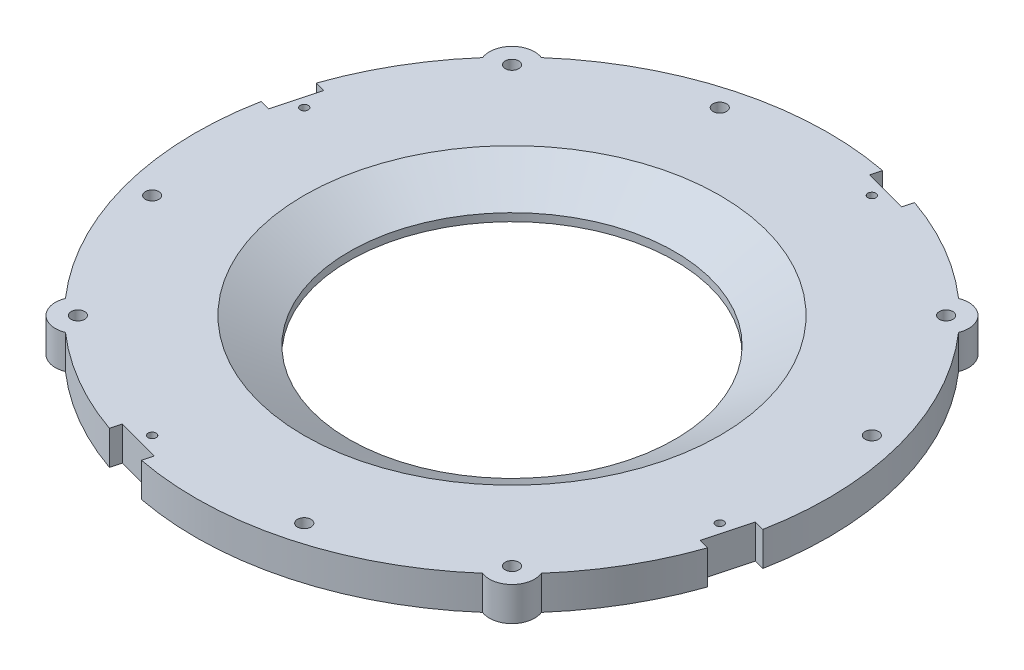
SolidWorks part; units mm, degrees
material "6061-T6 (SS)"
ref_plane "Front Plane" through (0, 0, 0) normal (0, 0, 1) x (1, 0, 0)
ref_plane "Top Plane" through (0, 0, 0) normal (0, 1, 0) x (1, 0, 0)
ref_plane "Right Plane" through (0, 0, 0) normal (1, 0, 0) x (0, 0, -1)
sketch "Sketch1" plane through (0, 0, 0) normal (0, 1, 0) x (1, 0, 0)
  line L0 (0, 88.9) -> (0, -88.9) construction
  line L1 (-88.9, 0) -> (88.9, 0) construction
  line L2 (-60.9759, -60.9759) -> (60.9759, 60.9759) construction
  line L3 (60.9759, -60.9759) -> (-60.9759, 60.9759) construction
  arc A0 (-66.8608, 58.5904) -> (-66.8608, -58.5904) centre (0, 0) ccw
  arc A1 (-58.5904, 66.8608) -> (-66.8608, 58.5904) centre (-60.9759, 60.9759) ccw
  arc A2 (66.8608, 58.5904) -> (58.5904, 66.8608) centre (60.9759, 60.9759) ccw
  arc A3 (58.5904, -66.8608) -> (66.8608, -58.5904) centre (60.9759, -60.9759) ccw
  arc A4 (-66.8608, -58.5904) -> (-58.5904, -66.8608) centre (-60.9759, -60.9759) ccw
  arc A5 (58.5904, 66.8608) -> (-58.5904, 66.8608) centre (0, 0) ccw
  arc A6 (66.8608, -58.5904) -> (66.8608, 58.5904) centre (0, 0) ccw
  arc A7 (-58.5904, -66.8608) -> (58.5904, -66.8608) centre (0, 0) ccw
  circle A8 centre (-60.9759, 60.9759) radius 1.905
  circle A9 centre (60.9759, 60.9759) radius 1.905
  circle A10 centre (60.9759, -60.9759) radius 1.905
  circle A11 centre (-60.9759, -60.9759) radius 1.905
  circle A12 centre (0, 0) radius 83.82 construction
  point P10 (0, 0)
  point P13 (0, 0)
  dimension "D1" = 177.8
  dimension "D3" = 12.7
  dimension "D4" = 3.81
  dimension "D7" = 167.64
  dimension "D2" = 90
  dimension "D5" = 45
  dimension "D6" = 172.466
extrude "Boss-Extrude1" add sketch "Sketch1" along normal blind 9.525
sketch "Sketch2" plane through (0, 9.525, 0) normal (0, 1, 0) x (1, 0, 0)
  circle A0 centre (0, 0) radius 45.72
extrude "Cut-Extrude1" cut sketch "Sketch2" against normal blind 12.7
sketch "Sketch4" plane through (0, 9.525, 0) normal (0, 1, 0) x (1, 0, 0)
  line L0 (0, 0) -> (-21.3655, 79.7372) construction
  line L2 (0, 0) -> (0, 123.2999) construction
  circle A0 centre (-21.3655, 79.7372) radius 1.905
  dimension "D1" = 3.81
  dimension "D2" = 82.55
  dimension "D3" = 15
ref_plane "Plane3" through (-62.8618, 0, -62.8618) normal (-0.7071, 0, -0.7071) x (0, -1, 0)
sketch "Sketch10" plane through (-62.8618, 0, -62.8618) normal (-0.7071, 0, -0.7071) x (0, -1, 0)
  line L0 (0, 0) -> (-9.652, 0) construction
  circle A1 centre (-4.826, 0) radius 0.6985
  dimension "D2" = 1.397
  dimension "D1" = 9.652
extrude "Cut-Extrude5" cut sketch "Sketch10" against normal blind 3.175
pattern_circular "CirPattern5" count 4 over 360 about axis through (0, 0, 0) along (0, 1, 0) of "Cut-Extrude5"
chamfer "Chamfer1" distance 12.7 angle 30 1 edges at (0, 9.525, 45.72)
extrude "Cut-Extrude6" cut sketch "Sketch4" against normal through all
pattern_circular "CirPattern6" count 4 over 360 about axis through (0, 0, 0) along (0, 1, 0) of "Cut-Extrude6"
sketch "Sketch13" plane through (0, 9.525, 0) normal (0, 1, 0) x (1, 0, 0)
  line L0 (0, 0) -> (0, 128.7148) construction
  line L1 (0, 0) -> (35.1918, 131.3375) construction
  circle A0 centre (21.3655, 79.7372) radius 1.1303
  dimension "D3" = 2.2606
  dimension "D1" = 15
  dimension "D2" = 82.55
extrude "Cut-Extrude7" cut sketch "Sketch13" against normal through all
pattern_circular "CirPattern7" count 4 over 360 about axis through (0, 0, 0) along (0, 1, 0) of "Cut-Extrude7"
ref_plane "Plane4" through (23.009, 0, -85.8708) normal (0.2588, 0, -0.9659) x (0, -1, 0)
sketch "Sketch14" plane through (23.009, 0, -85.8708) normal (0.2588, 0, -0.9659) x (0, -1, 0)
  line L1 (1.3545, -6.35) -> (-10.5978, -6.35)
  line L2 (1.3545, -6.35) -> (1.3545, 6.35)
  line L3 (1.3545, 6.35) -> (-10.5978, 6.35)
  line L4 (-10.5978, -6.35) -> (-10.5978, 6.35)
  line L5 (1.3545, -6.35) -> (-10.5978, 6.35) construction
  line L6 (1.3545, 6.35) -> (-10.5978, -6.35) construction
  point P0 (-4.6217, 0)
  dimension "D1" = 12.7
extrude "Cut-Extrude8" cut sketch "Sketch14" against normal blind 3.175
pattern_circular "CirPattern8" count 4 over 360 about axis through (0, 0, 0) along (0, 1, 0) of "Cut-Extrude8"
